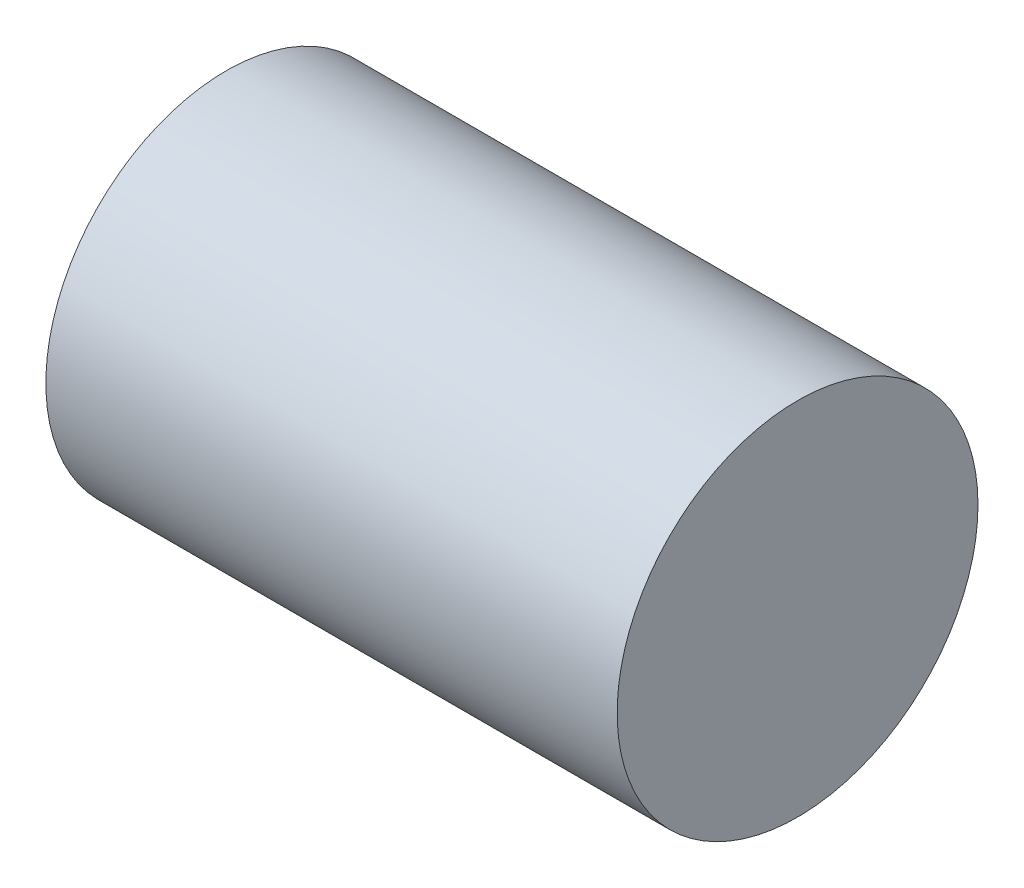
SolidWorks part; units mm, degrees
ref_plane "Front Plane" through (0, 0, 0) normal (0, 0, 1) x (1, 0, 0)
ref_plane "Top Plane" through (0, 0, 0) normal (0, 1, 0) x (1, 0, 0)
ref_plane "Right Plane" through (0, 0, 0) normal (1, 0, 0) x (0, 0, -1)
sketch "Sketch1" plane through (0, 0, 0) normal (1, 0, 0) x (0, 0, -1)
  circle A0 centre (0, 0) radius 3
extrude "Boss-Extrude1" add sketch "Sketch1" along normal blind 9.5
